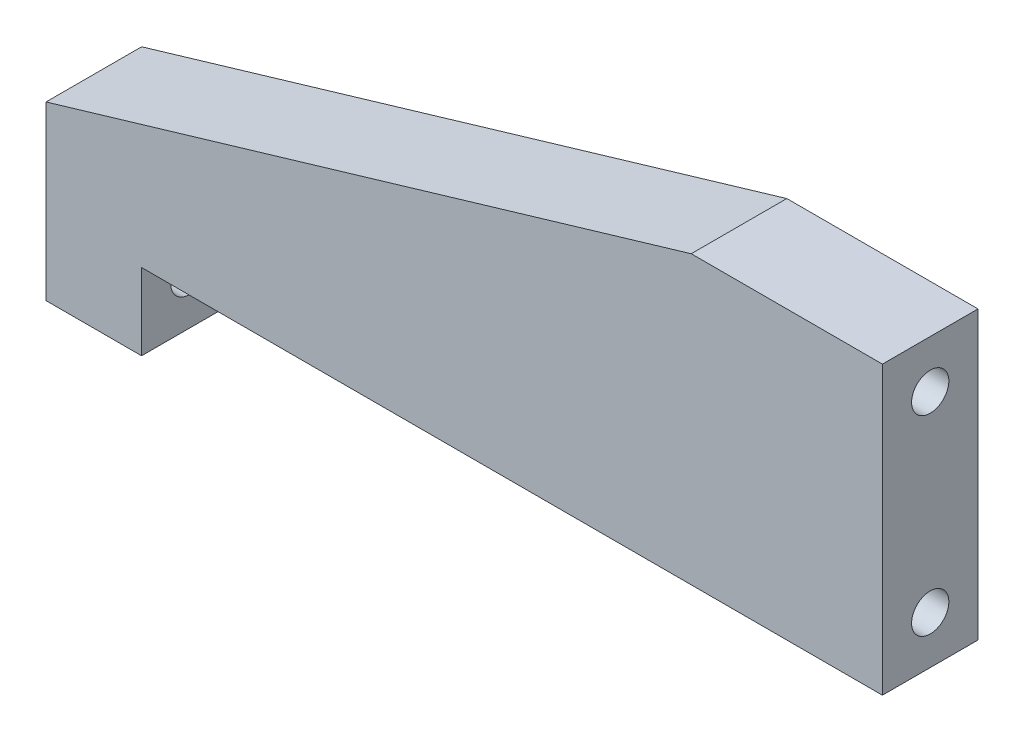
SolidWorks part; units mm, degrees
material "PLA Black"
ref_plane "Front Plane" through (0, 0, 0) normal (0, 0, 1) x (1, 0, 0)
ref_plane "Top Plane" through (0, 0, 0) normal (0, 1, 0) x (1, 0, 0)
ref_plane "Right Plane" through (0, 0, 0) normal (1, 0, 0) x (0, 0, -1)
sketch "Sketch1" plane through (0, 0, 0) normal (0, 0, 1) x (1, 0, 0)
  line L0 (-43.75, -15) -> (-43.75, -5)
  line L1 (-43.75, -15) -> (43.75, -15)
  line L2 (-43.75, -15) -> (-43.75, 15) construction
  line L3 (-43.75, 15) -> (43.75, 15) construction
  line L4 (43.75, -15) -> (43.75, 15)
  line L5 (-43.75, -5) -> (23.75, 15)
  line L6 (23.75, 15) -> (43.75, 15)
  point P4 (0, -15)
  point P6 (43.75, 0)
  dimension "D1" = 30
  dimension "D2" = 87.5
  dimension "D3" = 10
  dimension "D4" = 20
extrude "Extrude1" add sketch "Sketch1" along normal blind 10
hole_wizard "Ø4.0 (4) Diameter Hole1" positions "3DSketch1" profile "Sketch2" hole size "Ø4.0" standard "Ansi Metric"
sketch3d "3DSketch1"
  line L0 (-43.75, -5, 10) -> (-43.75, -5, 0) construction
  line L1 (-43.75, -5, 0) -> (-43.75, -15, 0) construction
  point P0 (-43.75, -10, 5)
  point P5 (-43.75, -5, 5)
  point P8 (-43.75, -10, 0)
  point P9 (43.75, -10, 5)
  point P15 (43.75, 10, 5)
  dimension "D1" = 20
sketch "Sketch2" plane through (-43.75, -10, 5) normal (0, 1, 0) x (0, 0, 1)
  line L0 (0, 0) -> (0, 15)
  line L1 (0, 15) -> (1.95, 15)
  line L2 (1.95, 15) -> (1.95, 0)
  line L5 (1.95, 0) -> (0, 0)
  line L10 (0, 15) -> (-1.95, 15) construction
  line L11 (0, -6.35) -> (0, 107.95) construction
  dimension "Hole Dia." = 3.9
  dimension "Hole Depth" = 15
  dimension "Drill Angle" = 180
sketch "Sketch3" plane through (0, 0, 0) normal (0, 0, 1) x (1, 0, 0)
  line L1 (-43.75, -15) -> (-33.75, -15)
  line L2 (-43.75, -15) -> (-43.75, -23)
  line L3 (-43.75, -23) -> (-33.75, -23)
  line L4 (-33.75, -15) -> (-33.75, -23)
  dimension "D1" = 8
  dimension "D2" = 10
extrude "Extrude2" add sketch "Sketch3" along normal up to surface (10 mm away) up to face at (4.75, -1, 10)
hole_wizard "Ø4.0 (4) Diameter Hole2" positions "3DSketch2" profile "Sketch4" hole size "Ø4.0" standard "Ansi Metric"
sketch3d "3DSketch2"
  line L0 (-43.75, -5, 5) -> (-43.75, -23, 5) construction
  line L1 (-43.75, -5, 10) -> (-43.75, -5, 0) construction
  line L2 (-43.75, -23, 10) -> (-43.75, -23, 0) construction
  circle A3 centre (-43.75, -10, 5) radius 1.95 construction
  point P0 (-43.75, -18, 5)
  point P23 (-45.7, -10, 5)
  dimension "D1" = 8
sketch "Sketch4" plane through (-43.75, -18, 5) normal (0, 1, 0) x (0, 0, 1)
  line L0 (0, 0) -> (0, 15)
  line L1 (0, 15) -> (1.95, 15)
  line L2 (1.95, 15) -> (1.95, 0)
  line L5 (1.95, 0) -> (0, 0)
  line L10 (0, 15) -> (-1.95, 15) construction
  line L11 (0, -6.35) -> (0, 107.95) construction
  dimension "Hole Dia." = 3.9
  dimension "Hole Depth" = 15
  dimension "Drill Angle" = 180
